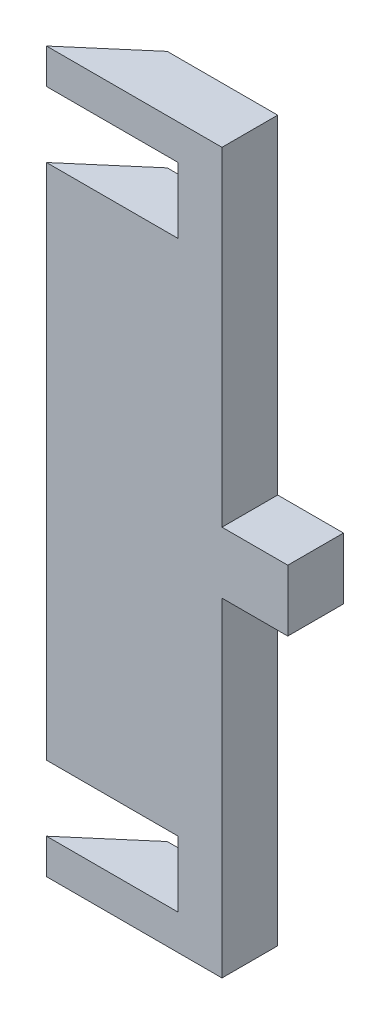
SolidWorks part; units mm, degrees
ref_plane "Alzado" through (0, 0, 0) normal (0, 0, 1) x (1, 0, 0)
ref_plane "Planta" through (0, 0, 0) normal (0, 1, 0) x (1, 0, 0)
ref_plane "Vista lateral" through (0, 0, 0) normal (1, 0, 0) x (0, 0, -1)
sketch "Croquis1" plane through (0, 0, 0) normal (0, 1, 0) x (1, 0, 0)
  line L0 (0, 0) -> (17.5008, 15)
  line L1 (17.5008, 15) -> (60, 15)
  line L2 (60, 15) -> (60, 0)
  line L3 (60, 0) -> (0, 0)
  dimension "D1" = 15
  dimension "D2" = 40.6
  dimension "D3" = 60
extrude "Saliente-Extruir1" add sketch "Croquis1" along normal blind 170
sketch "Croquis2" plane through (0, 0, -15) normal (0, 0, -1) x (-1, 0, 0)
  line L0 (-60, 85) -> (7.2827, 85) construction
  line L1 (-60, 0) -> (-52, 0)
  line L2 (-60, 0) -> (-60, 27)
  line L3 (-60, 27) -> (-52, 27)
  line L4 (-52, 0) -> (-52, 27)
  line L5 (-60, 170) -> (-60, 0) construction
  line L6 (-60, 0) -> (-17.5008, 0) construction
  line L7 (-52, 170) -> (-52, 143)
  line L8 (-60, 143) -> (-52, 143)
  line L9 (-60, 170) -> (-60, 143)
  line L10 (-60, 170) -> (-52, 170)
  dimension "D1" = 27
  dimension "D2" = 8
  dimension "D3" = 85
extrude "Cortar-Extruir1" cut sketch "Croquis2" against normal through all both and the other way through all
sketch "Croquis3" plane through (0, 0, -15) normal (0, 0, -1) x (-1, 0, 0)
  line L0 (-52, 170) -> (-17.5008, 170) construction
  line L1 (-46, 170) -> (-84.0651, 170)
  line L2 (-46, 170) -> (-46, -5.8261)
  line L3 (-46, -5.8261) -> (-84.0651, -5.8261)
  line L4 (-84.0651, 170) -> (-84.0651, -5.8261)
  line L5 (-52, 170) -> (-52, 143) construction
  dimension "D1" = 6
extrude "Cortar-Extruir2" cut sketch "Croquis3" against normal through all both and the other way through all
sketch "Croquis4" plane through (0, 0, 0) normal (0, -1, 0) x (1, 0, 0)
  line L0 (46, -15) -> (46, 0) construction
  line L1 (46, -12.7) -> (10.4677, -12.7)
  line L2 (46, -12.7) -> (46, -20.2368)
  line L3 (46, -20.2368) -> (10.4677, -20.2368)
  line L4 (10.4677, -12.7) -> (10.4677, -20.2368)
  line L5 (0, 0) -> (46, 0) construction
  dimension "D1" = 12.7
extrude "Cortar-Extruir3" cut sketch "Croquis4" against normal through all both and the other way through all
sketch "Croquis5" plane through (0, 0, -12.7) normal (0, 0, -1) x (-1, 0, 0)
  line L0 (-46, 170) -> (-46, 0) construction
  line L1 (-46, 6) -> (0, 6)
  line L2 (-46, 6) -> (-46, 0)
  line L3 (-46, 0) -> (0, 0)
  line L4 (0, 6) -> (0, 0)
  line L5 (-46, 170) -> (-14.8173, 170) construction
  line L6 (0, 170) -> (0, 0) construction
  line L8 (-46, 6) -> (-46, 81)
  line L9 (-46, 81) -> (-40, 81)
  line L10 (-40, 6) -> (-40, 81)
  line L11 (-46, 170) -> (-40, 170)
  line L12 (-46, 170) -> (-46, 95)
  line L13 (-46, 95) -> (-40, 95)
  line L14 (-40, 170) -> (-40, 95)
  line L15 (-14.8173, 170) -> (0, 170) construction
  line L16 (0, 14) -> (-30, 14)
  line L17 (0, 14) -> (0, 29)
  line L18 (0, 29) -> (-30, 29)
  line L19 (-30, 14) -> (-30, 29)
  line L20 (0, 147) -> (-30, 147)
  line L21 (0, 147) -> (0, 162)
  line L22 (0, 162) -> (-30, 162)
  line L23 (-30, 147) -> (-30, 162)
  line M12 (-14.8173, 170) -> (-46, 170)
  line M13 (-46, 170) -> (-46, 0)
  line M14 (-46, 0) -> (-14.8173, 0)
  line M15 (-14.8173, 0) -> (-14.8173, 170)
  dimension "D1" = 164
  dimension "D2" = 40
  dimension "D3" = 40
  dimension "D4" = 75
  dimension "D5" = 75
  dimension "D6" = 15
  dimension "D7" = 15
  dimension "D8" = 10
  dimension "D9" = 10
  dimension "D10" = 8
  dimension "D11" = 8
extrude "Cortar-Extruir4" cut sketch "Croquis5" against normal through all both and the other way through all contours L17 L18 L16 M15 | L19 L16 L18 M15 | L1 L10 L9 M13 | L1 M13 M14 M15 | L4 L1 L3 M15 | L14 L13 M12 M13 | L23 L20 L22 M15 | L21 L22 L20 M15
sketch "Croquis6" plane through (0, 0, -12.7) normal (0, 0, -1) x (-1, 0, 0)
  line L0 (-40, 95) -> (-40, 170) construction
  line L1 (-46, 95) -> (-55, 95)
  line L2 (-46, 95) -> (-46, 81)
  line L3 (-46, 81) -> (-55, 81)
  line L4 (-55, 95) -> (-55, 81)
  dimension "D1" = 15
extrude "Saliente-Extruir2" add sketch "Croquis6" against normal up to vertex (12.7 mm away) up to point (46, 95, 0)
